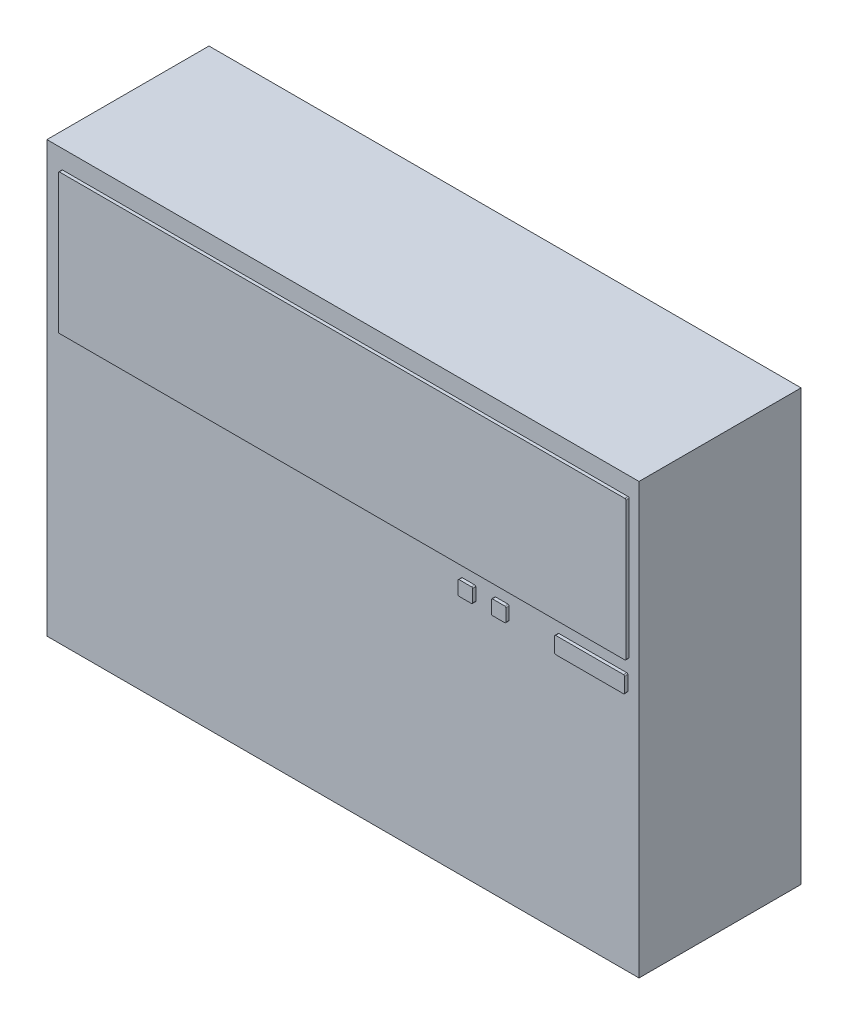
SolidWorks part; units mm, degrees
ref_plane "Front" through (0, 0, 0) normal (0, 0, 1) x (1, 0, 0)
ref_plane "Top" through (0, 0, 0) normal (0, 1, 0) x (1, 0, 0)
ref_plane "Right" through (0, 0, 0) normal (1, 0, 0) x (0, 0, -1)
sketch "Sketch1" plane through (0, 0, 0) normal (0, 0, 1) x (1, 0, 0)
  line L8 (-74.9024, 175.4012) -> (-74.9024, 74.3092)
  line L9 (-74.9024, 74.3092) -> (64.2896, 74.3092)
  line L10 (64.2896, 74.3092) -> (64.2896, 175.4012)
  line L11 (64.2896, 175.4012) -> (-74.9024, 175.4012)
  line L12 (-74.9024, 175.4012) -> (-74.9024, 74.3092)
  line L13 (-74.9024, 74.3092) -> (64.2896, 74.3092)
  line L14 (64.2896, 74.3092) -> (64.2896, 175.4012)
  line L15 (64.2896, 175.4012) -> (-74.9024, 175.4012)
  dimension "D1" = 0.254
extrude "Base-Extrude" add sketch "Sketch1" along normal up to vertex
sketch "Sketch2" plane through (0, 0, 38.1) normal (0, 0, 1) x (1, 0, 0)
  line L1 (-71.194, 171.0435) -> (61.725, 171.0435)
  line L2 (-71.448, 170.7895) -> (-71.448, 138.4112)
  line L3 (-71.194, 138.1572) -> (61.725, 138.1572)
  line L4 (61.979, 170.7895) -> (61.979, 138.4112)
  line L5 (45.4739, 135.0252) -> (61.4091, 135.0252)
  line L6 (45.2199, 134.7712) -> (45.2199, 131.3641)
  line L7 (45.4739, 131.1101) -> (61.4091, 131.1101)
  line L8 (61.6631, 134.7712) -> (61.6631, 131.3641)
  line L9 (22.7668, 135.0252) -> (25.6658, 135.0252)
  line L10 (22.5128, 134.7712) -> (22.5128, 131.8721)
  line L11 (22.7668, 131.6181) -> (25.6658, 131.6181)
  line L12 (25.9198, 134.7712) -> (25.9198, 131.8721)
  line L13 (30.5968, 135.0252) -> (33.4959, 135.0252)
  line L14 (30.3428, 134.7712) -> (30.3428, 131.8721)
  line L15 (30.5968, 131.6181) -> (33.4959, 131.6181)
  line L16 (33.7499, 134.7712) -> (33.7499, 131.8721)
  arc A0 (61.4091, 135.0252) -> (61.6631, 134.7712) centre (61.4091, 134.7712) cw
  arc A1 (61.4091, 131.1101) -> (61.6631, 131.3641) centre (61.4091, 131.3641) ccw
  arc A2 (45.2199, 131.3641) -> (45.4739, 131.1101) centre (45.4739, 131.3641) ccw
  arc A3 (45.4739, 135.0252) -> (45.2199, 134.7712) centre (45.4739, 134.7712) ccw
  arc A4 (61.725, 138.1572) -> (61.979, 138.4112) centre (61.725, 138.4112) ccw
  arc A5 (61.725, 171.0435) -> (61.979, 170.7895) centre (61.725, 170.7895) cw
  arc A6 (33.4959, 135.0252) -> (33.7499, 134.7712) centre (33.4959, 134.7712) cw
  arc A7 (33.4959, 131.6181) -> (33.7499, 131.8721) centre (33.4959, 131.8721) ccw
  arc A8 (30.3428, 131.8721) -> (30.5968, 131.6181) centre (30.5968, 131.8721) ccw
  arc A9 (30.5968, 135.0252) -> (30.3428, 134.7712) centre (30.5968, 134.7712) ccw
  arc A10 (25.6658, 131.6181) -> (25.9198, 131.8721) centre (25.6658, 131.8721) ccw
  arc A11 (25.6658, 135.0252) -> (25.9198, 134.7712) centre (25.6658, 134.7712) cw
  arc A12 (22.7668, 135.0252) -> (22.5128, 134.7712) centre (22.7668, 134.7712) ccw
  arc A13 (22.5128, 131.8721) -> (22.7668, 131.6181) centre (22.7668, 131.8721) ccw
  arc A14 (-71.448, 138.4112) -> (-71.194, 138.1572) centre (-71.194, 138.4112) ccw
  arc A15 (-71.194, 171.0435) -> (-71.448, 170.7895) centre (-71.194, 170.7895) ccw
  dimension "D1" = 0.254
extrude "Boss-Extrude1" add sketch "Sketch2" along normal blind 0.762
